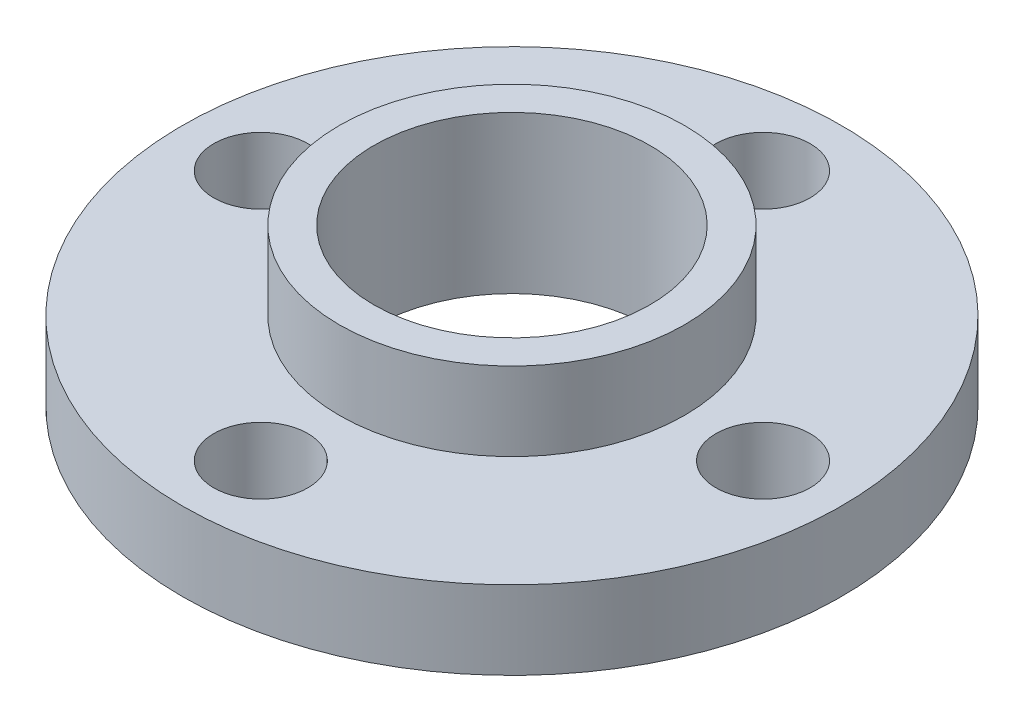
SolidWorks part; units mm, degrees
material "1060 Сплав"
ref_plane "Спереди" through (0, 0, 0) normal (0, 0, 1) x (1, 0, 0)
ref_plane "Сверху" through (0, 0, 0) normal (0, 1, 0) x (1, 0, 0)
ref_plane "Справа" through (0, 0, 0) normal (1, 0, 0) x (0, 0, -1)
sketch "Эскиз1" plane through (0, 0, 0) normal (0, 1, 0) x (1, 0, 0)
  circle A0 centre (0, 0) radius 10.5
  circle A5 centre (0, 0) radius 4.4
  dimension "D1" = 21
  dimension "D10" = 8.8
extrude "Бобышка-Вытянуть1" add sketch "Эскиз1" along normal blind 2.5
sketch "Эскиз2" plane through (0, 2.5, 0) normal (0, 1, 0) x (1, 0, 0)
  circle A0 centre (0, 0) radius 4.4
  circle A1 centre (0, 0) radius 5.5
  dimension "D1" = 11
  dimension "D2" = 8.8
extrude "Бобышка-Вытянуть2" add sketch "Эскиз2" along normal blind 2.5
sketch "Эскиз3" plane through (0, 2.5, 0) normal (0, 1, 0) x (1, 0, 0)
  circle A0 centre (-8, 0) radius 1.5
  dimension "D1" = 3
  dimension "D2" = 8
extrude "Вырез-Вытянуть1" cut sketch "Эскиз3" against normal through all
pattern_circular "Круговой массив2" count 4 over 360 about axis through (0, 0, 0) along (0, 1, 0) of "Вырез-Вытянуть1"
